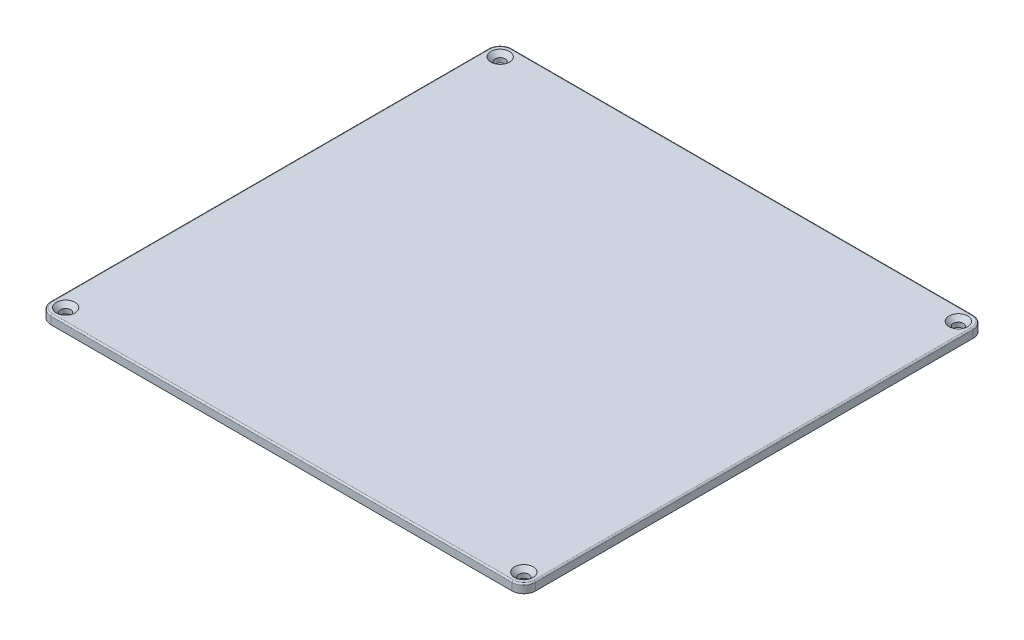
SolidWorks part; units mm, degrees
ref_plane "Front Plane" through (0, 0, 0) normal (0, 0, 1) x (1, 0, 0)
ref_plane "Top Plane" through (0, 0, 0) normal (0, 1, 0) x (1, 0, 0)
ref_plane "Right Plane" through (0, 0, 0) normal (1, 0, 0) x (0, 0, -1)
sketch "Sketch1" plane through (0, 0, 0) normal (0, 1, 0) x (1, 0, 0)
  line L1 (0, 0) -> (164, 0)
  line L2 (0, 0) -> (0, 156)
  line L3 (0, 156) -> (164, 156)
  line L4 (164, 0) -> (164, 156)
  dimension "D1" = 156
  dimension "D2" = 164
extrude "Boss-Extrude1" add sketch "Sketch1" along normal blind 3
sketch "Sketch2" plane through (0, 0, 0) normal (0, -1, 0) x (1, 0, 0)
  line L0 (164, 0) -> (164, -156) construction
  line L1 (10, -3.5) -> (154, -3.5)
  line L2 (3.5, -10) -> (3.5, -146)
  line L3 (10, -152.5) -> (154, -152.5)
  line L4 (160.5, -10) -> (160.5, -146)
  line L5 (164, -156) -> (0, -156) construction
  line L6 (0, -156) -> (0, 0) construction
  line L7 (0, 0) -> (164, 0) construction
  arc A0 (160.5, -146) -> (154, -152.5) centre (160.5, -152.5) ccw
  arc A1 (3.5, -146) -> (10, -152.5) centre (3.5, -152.5) cw
  arc A2 (160.5, -10) -> (154, -3.5) centre (160.5, -3.5) cw
  arc A3 (10, -3.5) -> (3.5, -10) centre (3.5, -3.5) cw
  dimension "D5" = 6.5
  dimension "D6" = 6.5
  dimension "D7" = 6.5
  dimension "D8" = 6.5
  dimension "D1" = 3.5
  dimension "D2" = 3.5
  dimension "D3" = 3.5
  dimension "D4" = 3.5
  dimension "D9" = 144
  dimension "D10" = 136
  dimension "D11" = 144
  dimension "D12" = 136
  dimension "D13" = 10
  dimension "D14" = 10
  dimension "D15" = 3.5
  dimension "D16" = 3.5
extrude "Boss-Extrude2" add sketch "Sketch2" along normal blind 3 contours L4 A0 L3 A1 L2 A3 L1 A2
sketch "Sketch4" plane through (0, -3, 0) normal (0, -1, 0) x (1, 0, 0)
  line L8 (151.4861, -6.5) -> (12.5139, -6.5)
  line L9 (6.5, -12.5139) -> (6.5, -143.4861)
  line L10 (12.5139, -149.5) -> (151.4861, -149.5)
  line L11 (157.5, -143.4861) -> (157.5, -12.5139)
  line L12 (151.4861, -6.5) -> (12.5139, -6.5)
  line L13 (6.5, -12.5139) -> (6.5, -143.4861)
  line L14 (12.5139, -149.5) -> (151.4861, -149.5)
  line L15 (157.5, -143.4861) -> (157.5, -12.5139)
  arc A8 (151.4861, -6.5) -> (157.5, -12.5139) centre (160.5, -3.5) ccw
  arc A9 (6.5, -12.5139) -> (12.5139, -6.5) centre (3.5, -3.5) ccw
  arc A10 (12.5139, -149.5) -> (6.5, -143.4861) centre (3.5, -152.5) ccw
  arc A11 (157.5, -143.4861) -> (151.4861, -149.5) centre (160.5, -152.5) ccw
  arc A12 (151.4861, -6.5) -> (157.5, -12.5139) centre (160.5, -3.5) ccw
  arc A13 (6.5, -12.5139) -> (12.5139, -6.5) centre (3.5, -3.5) ccw
  arc A14 (12.5139, -149.5) -> (6.5, -143.4861) centre (3.5, -152.5) ccw
  arc A15 (157.5, -143.4861) -> (151.4861, -149.5) centre (160.5, -152.5) ccw
  dimension "D1" = 3
extrude "Cut-Extrude1" cut sketch "Sketch4" against normal blind 3
fillet "Fillet1" radius 4 4 edges at (0, 1.5, 0) (0, 1.5, -156) (164, 1.5, -156) (164, 1.5, 0)
fillet "Fillet2" radius 1 8 edges at (154, -1.5, -3.5) (160.5, -1.5, -10) (160.5, -1.5, -146) (154, -1.5, -152.5) (10, -1.5, -152.5) (3.5, -1.5, -146) (3.5, -1.5, -10) (10, -1.5, -3.5)
hole_wizard "CSK for M3 Countersunk Flat Head Screw1" positions "Sketch6" profile "Sketch7" countersink size "M3" standard "ISO" end condition through all
sketch "Sketch6" plane through (0, 3, 0) normal (0, 1, 0) x (1, 0, 0)
  line L0 (164, 4) -> (164, 152) construction
  line L1 (160, 156) -> (4, 156) construction
  line L2 (4, 0) -> (160, 0) construction
  line L3 (0, 152) -> (0, 4) construction
  point P0 (159.5, 4.5)
  point P2 (4.5, 4.5)
  point P4 (4.5, 151.5)
  point P6 (159.5, 151.5)
  dimension "D1" = 4.5
  dimension "D2" = 4.5
  dimension "D3" = 4.5
  dimension "D4" = 4.5
sketch "Sketch7" plane through (159.5, 3, -4.5) normal (1, 0, 0) x (0, 0, 1)
  line L0 (0, 0) -> (0, 6)
  line L1 (0, 6) -> (1.7, 6)
  line L2 (1.7, 6) -> (1.7, 1.45)
  line L3 (1.7, 1.45) -> (3.15, 0)
  line L5 (3.15, 0) -> (0, 0)
  line L6 (-1.7, 1.45) -> (-3.15, 0) construction
  line L11 (0, -6.35) -> (0, 107.95) construction
  dimension "Thru Hole Dia." = 3.4
  dimension "Thru Hole Depth" = 6
  dimension "Near C'Sink Dia." = 6.3
  dimension "Near C'Sink Angle" = 90
fillet "Fillet3" radius 0.5 8 edges at (1.1716, 3, -154.8284) (82, 3, -156) (162.8284, 3, -154.8284) (164, 3, -78) (162.8284, 3, -1.1716) (82, 3, 0) (1.1716, 3, -1.1716) (0, 3, -78)
